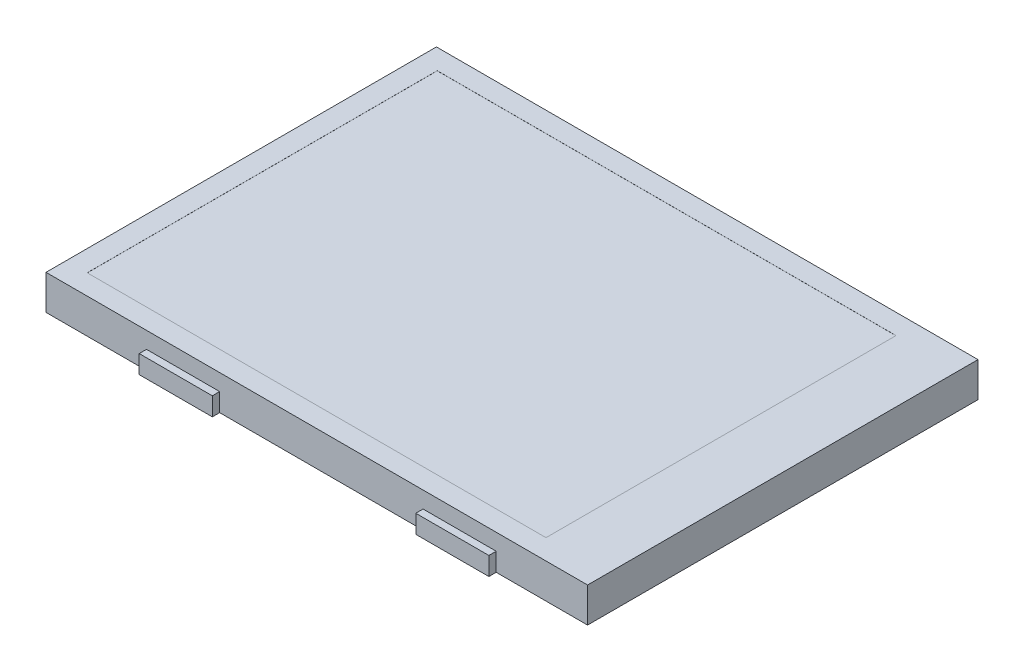
SolidWorks part; units mm, degrees
ref_plane "Front Plane" through (0, 0, 0) normal (0, 0, 1) x (1, 0, 0)
ref_plane "Top Plane" through (0, 0, 0) normal (0, 1, 0) x (1, 0, 0)
ref_plane "Right Plane" through (0, 0, 0) normal (1, 0, 0) x (0, 0, -1)
sketch "Sketch1" plane through (0, 0, 0) normal (0, 1, 0) x (1, 0, 0)
  line L1 (-29.63, -21.36) -> (29.63, -21.36)
  line L2 (-29.63, -21.36) -> (-29.63, 21.36)
  line L3 (-29.63, 21.36) -> (29.63, 21.36)
  line L4 (29.63, -21.36) -> (29.63, 21.36)
  line L5 (-29.63, -21.36) -> (29.63, 21.36) construction
  line L6 (-29.63, 21.36) -> (29.63, -21.36) construction
  point P0 (0, 0)
  dimension "D1" = 59.26
  dimension "D2" = 42.72
extrude "Boss-Extrude1" add sketch "Sketch1" along normal blind 3.8
sketch "Sketch2" plane through (0, 0, 21.36) normal (0, 0, 1) x (1, 0, 0)
  line L0 (-29.63, 0) -> (29.63, 0) construction
  line L1 (-18.63, 2) -> (-10.63, 2)
  line L2 (-18.63, 2) -> (-18.63, 0)
  line L3 (-18.63, 0) -> (-10.63, 0)
  line L4 (-10.63, 2) -> (-10.63, 0)
  line L5 (11.63, 2) -> (19.63, 2)
  line L6 (11.63, 2) -> (11.63, 0)
  line L7 (11.63, 0) -> (19.63, 0)
  line L8 (19.63, 2) -> (19.63, 0)
  line L9 (-29.63, 3.8) -> (-29.63, 0) construction
  dimension "D1" = 8
  dimension "D2" = 8
  dimension "D3" = 2
  dimension "D4" = 11
  dimension "D5" = 30.26
extrude "Boss-Extrude2" add sketch "Sketch2" along normal blind 0.8
sketch "Sketch3" plane through (0, 0, -21.36) normal (0, 0, -1) x (-1, 0, 0)
  line L0 (18.63, 2) -> (18.63, 0) construction
  line L1 (18.63, 0) -> (10.63, 0) construction
  line L2 (10.63, 0) -> (10.63, 2) construction
  line L3 (10.63, 2) -> (18.63, 2) construction
  line L4 (-11.63, 2) -> (-11.63, 0) construction
  line L5 (-11.63, 0) -> (-19.63, 0) construction
  line L6 (-19.63, 0) -> (-19.63, 2) construction
  line L7 (-19.63, 2) -> (-11.63, 2) construction
  line L8 (18.63, 2) -> (18.63, 0)
  line L9 (18.63, 0) -> (10.63, 0)
  line L10 (10.63, 0) -> (10.63, 2)
  line L11 (10.63, 2) -> (18.63, 2)
  line L12 (-11.63, 2) -> (-11.63, 0)
  line L13 (-11.63, 0) -> (-19.63, 0)
  line L14 (-19.63, 0) -> (-19.63, 2)
  line L15 (-19.63, 2) -> (-11.63, 2)
extrude "Boss-Extrude3" add sketch "Sketch3" along normal blind 0.8
sketch "Sketch4" plane through (0, 3.8, 0) normal (0, 1, 0) x (1, 0, 0)
  line L0 (-29.63, 21.36) -> (-29.63, -21.36) construction
  line L1 (-27.33, 19.15) -> (22.87, 19.15)
  line L2 (-27.33, 19.15) -> (-27.33, -19.15)
  line L3 (-27.33, -19.15) -> (22.87, -19.15)
  line L4 (22.87, 19.15) -> (22.87, -19.15)
  point P6 (-27.33, 0)
  point P7 (-29.63, 0)
  dimension "D1" = 50.2
  dimension "D2" = 38.3
  dimension "D3" = 2.3
extrude "Cut-Extrude1" cut sketch "Sketch4" against normal blind 0.01
sketch "Sketch5" plane through (0, 3.79, 0) normal (0, 1, 0) x (1, 0, 0)
  line L0 (295.1014, 309.5928) -> (1555.1014, 309.5928) construction
